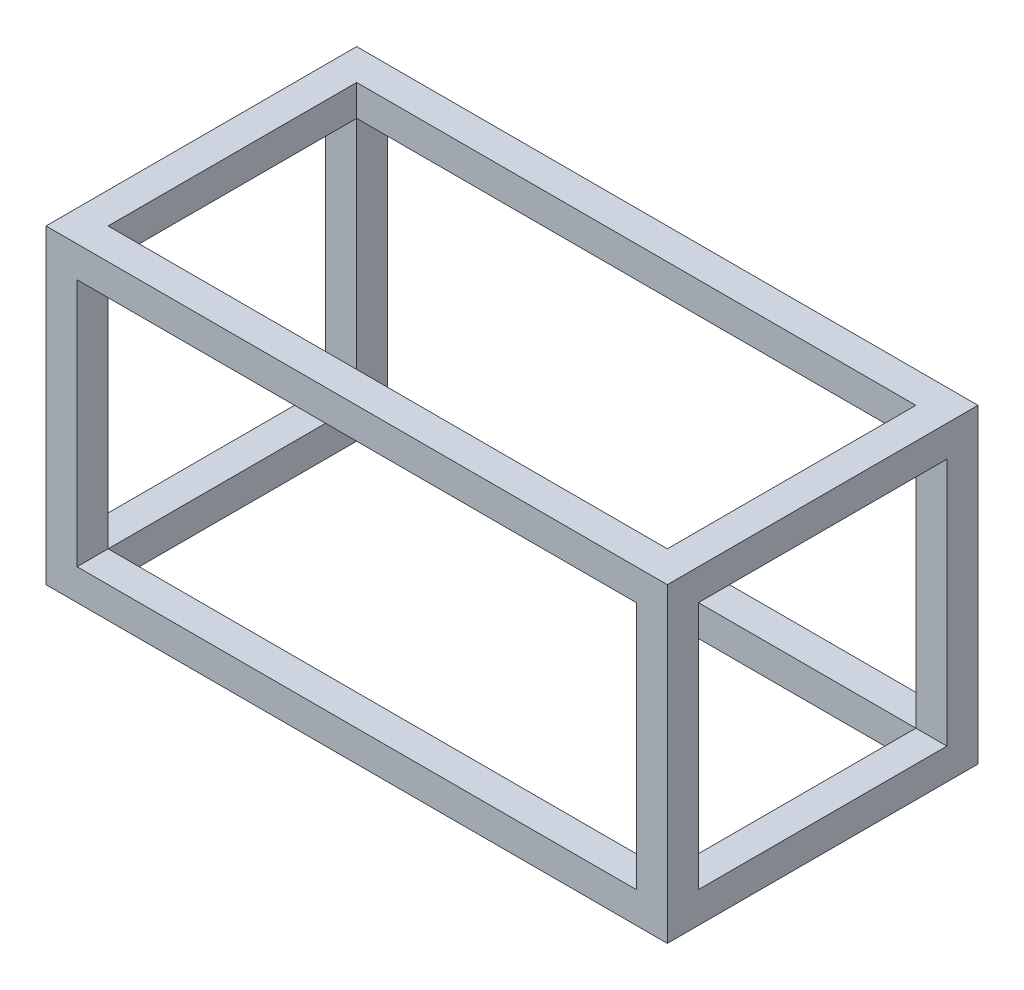
SolidWorks part; units mm, degrees
ref_plane "Front Plane" through (0, 0, 0) normal (0, 0, 1) x (1, 0, 0)
ref_plane "Top Plane" through (0, 0, 0) normal (0, 1, 0) x (1, 0, 0)
ref_plane "Right Plane" through (0, 0, 0) normal (1, 0, 0) x (0, 0, -1)
sketch "Sketch1" plane through (0, 0, 0) normal (0, 1, 0) x (1, 0, 0)
  line L1 (0, 0) -> (100, 0)
  line L2 (0, 0) -> (0, 50)
  line L3 (0, 50) -> (100, 50)
  line L4 (100, 0) -> (100, 50)
  line L5 (5, 45) -> (95, 45)
  line L6 (5, 45) -> (5, 5)
  line L7 (5, 5) -> (95, 5)
  line L8 (95, 45) -> (95, 5)
  dimension "D1" = 50
  dimension "D2" = 100
  dimension "D3" = 5
  dimension "D4" = 5
  dimension "D5" = 5
  dimension "D6" = 5
extrude "Boss-Extrude1" add sketch "Sketch1" along normal blind 50
sketch "Sketch2" plane through (100, 0, 0) normal (1, 0, 0) x (0, 0, -1)
  line L1 (0, 50) -> (50, 50)
  line L2 (0, 50) -> (0, 0)
  line L3 (0, 0) -> (50, 0)
  line L4 (50, 50) -> (50, 0)
  line L5 (5, 45) -> (45, 45)
  line L6 (5, 45) -> (5, 5)
  line L7 (5, 5) -> (45, 5)
  line L8 (45, 45) -> (45, 5)
  dimension "D1" = 5
  dimension "D2" = 5
  dimension "D3" = 5
  dimension "D4" = 5
extrude "Cut-Extrude1" cut sketch "Sketch2" against normal through all contours L6 L5 L8 L7
sketch "Sketch3" plane through (0, 0, 0) normal (0, 0, 1) x (1, 0, 0)
  line L1 (0, 50) -> (100, 50)
  line L2 (0, 50) -> (0, 0)
  line L3 (0, 0) -> (100, 0)
  line L4 (100, 50) -> (100, 0)
  line L5 (5, 45) -> (95, 45)
  line L6 (5, 45) -> (5, 5)
  line L7 (5, 5) -> (95, 5)
  line L8 (95, 45) -> (95, 5)
  dimension "D1" = 5
  dimension "D2" = 5
  dimension "D3" = 5
  dimension "D4" = 5
extrude "Cut-Extrude2" cut sketch "Sketch3" against normal through all contours L6 L5 L8 L7
